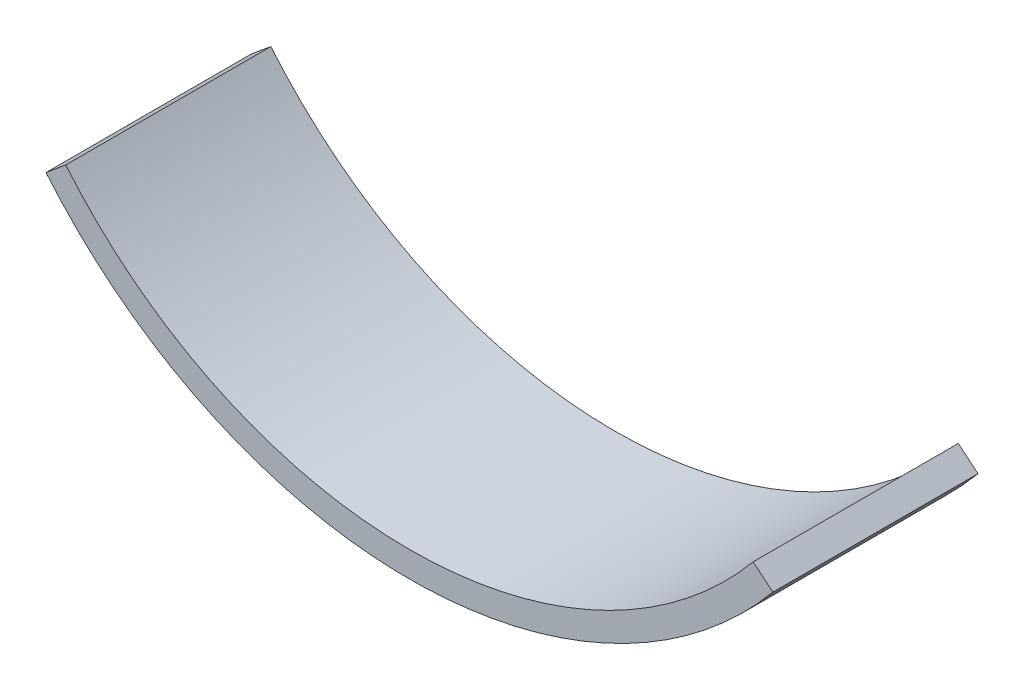
SolidWorks part; units mm, degrees
material "Natural Rubber"
ref_plane "Front Plane" through (0, 0, 0) normal (0, 0, 1) x (1, 0, 0)
ref_plane "Top Plane" through (0, 0, 0) normal (0, 1, 0) x (1, 0, 0)
ref_plane "Right Plane" through (0, 0, 0) normal (1, 0, 0) x (0, 0, -1)
sketch "Sketch1" plane through (0, 0, 0) normal (0, 0, 1) x (1, 0, 0)
  line L0 (0, 0) -> (2.4404, 2.031)
  line L1 (87.5596, 2.031) -> (90, 0)
  line L2 (90, 0) -> (93.1984, 3.8432) construction
  line L3 (0, 0) -> (-3.1984, 3.8432) construction
  arc A0 (0, 0) -> (90, 0) centre (45, 37.4502) ccw
  arc A1 (2.4404, 2.031) -> (87.5596, 2.031) centre (45, 37.4502) ccw
  dimension "D1" = 58.545
  dimension "D3" = 55.37
  dimension "D2" = 90
  dimension "D4" = 5
  dimension "D5" = 5
extrude "Boss-Extrude1" add sketch "Sketch1" along normal blind 25.4
